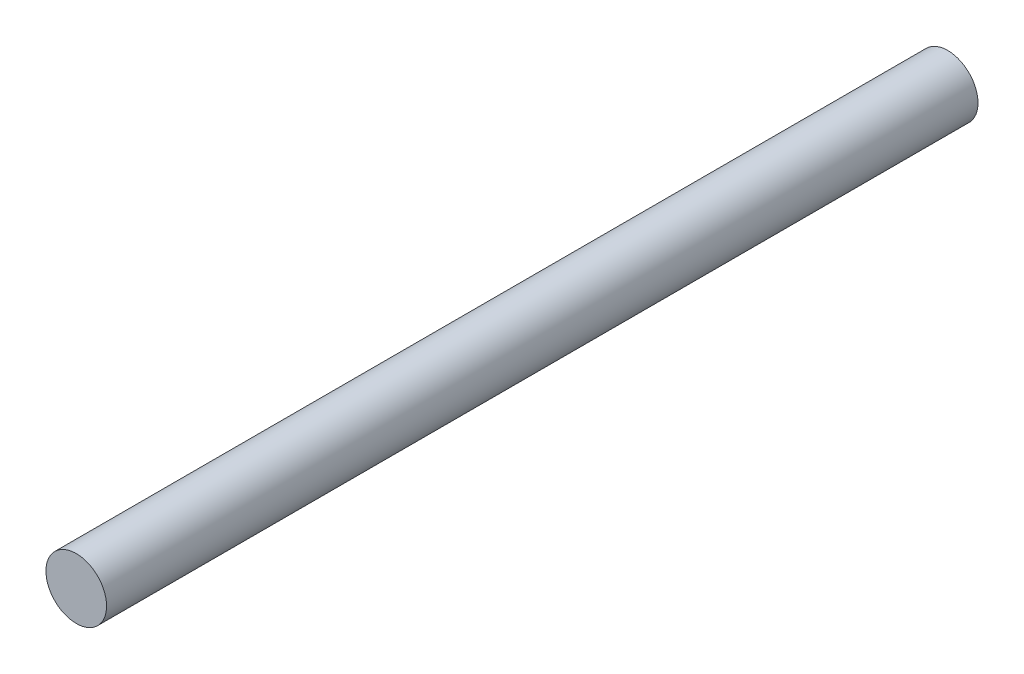
SolidWorks part; units mm, degrees
ref_plane "Front Plane" through (0, 0, 0) normal (0, 0, 1) x (1, 0, 0)
ref_plane "Top Plane" through (0, 0, 0) normal (0, 1, 0) x (1, 0, 0)
ref_plane "Right Plane" through (0, 0, 0) normal (1, 0, 0) x (0, 0, -1)
sketch "Sketch1" plane through (0, 0, 0) normal (0, 0, 1) x (1, 0, 0)
  circle A0 centre (0, 0) radius 4
extrude "Boss-Extrude1" add sketch "Sketch1" along normal blind 115
